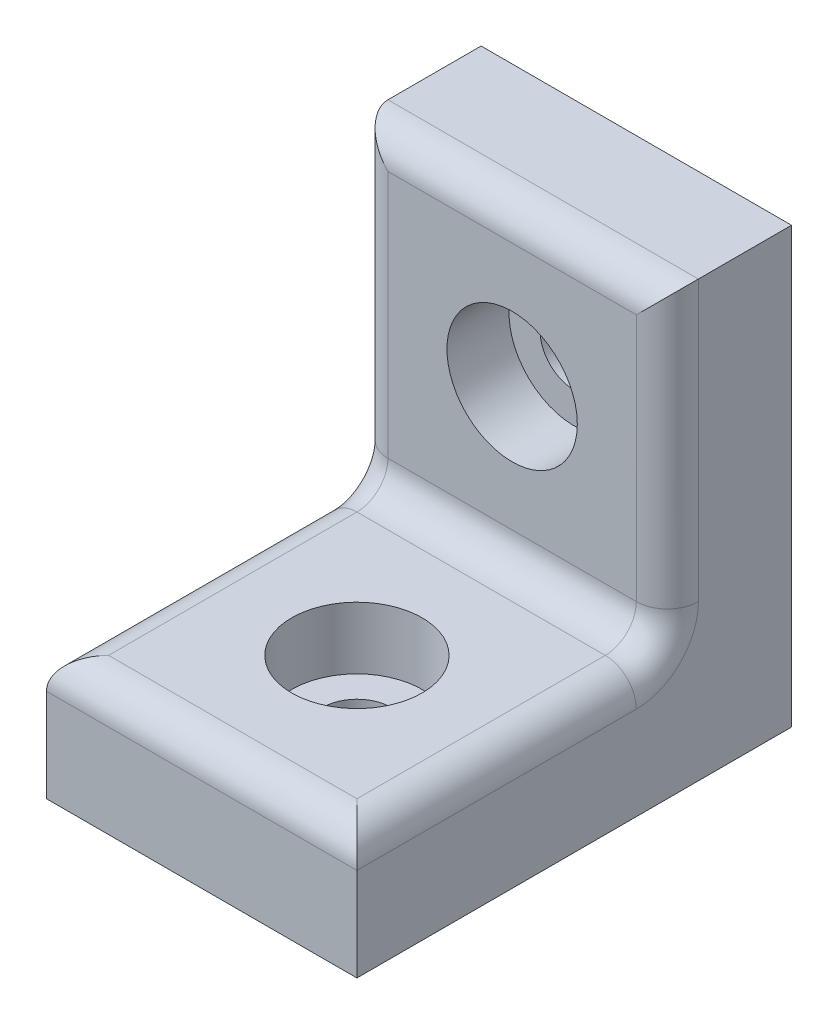
SolidWorks part; units mm, degrees
ref_plane "Plan de face" through (0, 0, 0) normal (0, 0, 1) x (1, 0, 0)
ref_plane "Plan de dessus" through (0, 0, 0) normal (0, 1, 0) x (1, 0, 0)
ref_plane "Plan de droite" through (0, 0, 0) normal (1, 0, 0) x (0, 0, -1)
sketch "Esquisse1" plane through (0, 0, 0) normal (0, 0, 1) x (1, 0, 0)
  line L1 (-5, 14) -> (5, 14)
  line L2 (-5, 14) -> (-5, 0)
  line L3 (-5, 0) -> (5, 0)
  line L4 (5, 14) -> (5, 0)
  dimension "D1" = 10
  dimension "D2" = 14
  dimension "D3" = 5
extrude "Boss.-Extru.1" add sketch "Esquisse1" along normal blind 4
sketch "Esquisse2" plane through (0, 0, 4) normal (0, 0, 1) x (1, 0, 0)
  line L0 (5, 0) -> (5, 14) construction
  line L1 (-5, 0) -> (5, 0)
  line L2 (-5, 0) -> (-5, 4)
  line L3 (-5, 4) -> (5, 4)
  line L4 (5, 0) -> (5, 4)
  dimension "D1" = 4
extrude "Boss.-Extru.2" add sketch "Esquisse2" along normal blind 10
sketch "Esquisse3" plane through (0, 0, 4) normal (0, 0, 1) x (1, 0, 0)
  line L0 (5, 14) -> (-5, 14) construction
  line L1 (-5, 14) -> (-5, 4) construction
  circle A0 centre (0, 9) radius 1.1
  point P2 (0, 14)
  point P3 (-5, 9)
  dimension "D1" = 2.2
extrude "Enlèv. mat.-Extru.1" cut sketch "Esquisse3" against normal through all
fillet "Congé1" radius 1 7 edges at (0, 4, 4) (5, 9, 4) (-5, 9, 4) (0, 4, 14) (5, 4, 9) (-5, 4, 9) (0, 14, 4)
sketch "Esquisse4" plane through (0, 4, 0) normal (0, 1, 0) x (1, 0, 0)
  line L0 (5, -14) -> (-5, -14) construction
  line L1 (-5, -14) -> (-5, -4) construction
  circle A0 centre (0, -9) radius 1.1
  point P0 (0, -14)
  point P1 (-5, -9)
  dimension "D1" = 2.2
extrude "Enlèv. mat.-Extru.2" cut sketch "Esquisse4" against normal through all
sketch "Esquisse5" plane through (0, 0, 4) normal (0, 0, 1) x (1, 0, 0)
  circle A0 centre (0, 9) radius 2.1
  dimension "D1" = 4.2
extrude "Enlèv. mat.-Extru.3" cut sketch "Esquisse5" against normal blind 2
sketch "Esquisse6" plane through (0, 4, 0) normal (0, 1, 0) x (1, 0, 0)
  circle A0 centre (0, -9) radius 2.1
  dimension "D1" = 4.2
extrude "Enlèv. mat.-Extru.4" cut sketch "Esquisse6" against normal blind 2
